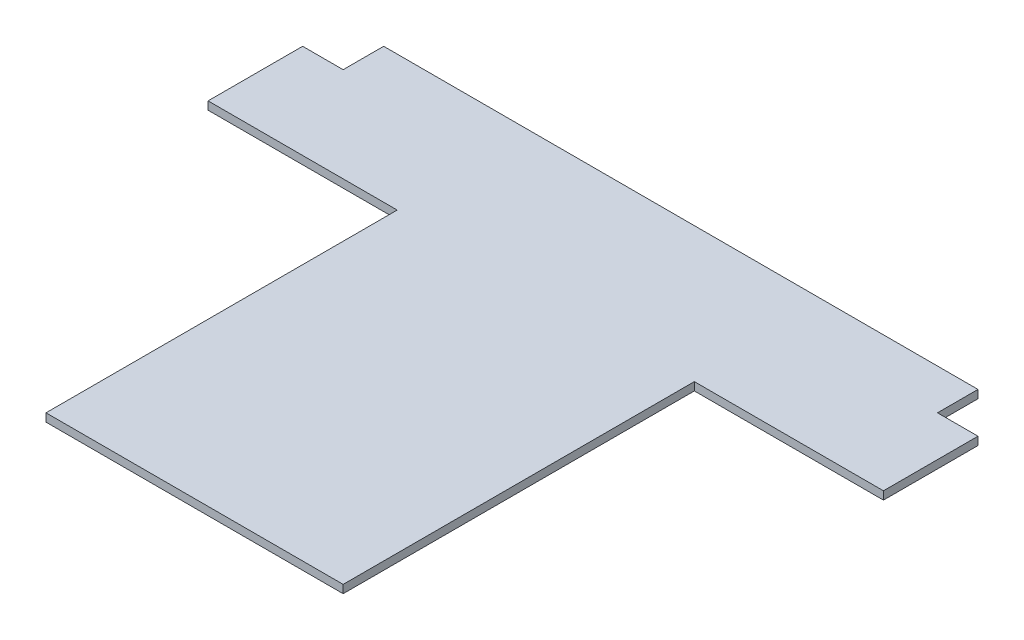
SolidWorks part; units mm, degrees
ref_plane "Plano frontal" through (0, 0, 0) normal (0, 0, 1) x (1, 0, 0)
ref_plane "Plano superior" through (0, 0, 0) normal (0, 1, 0) x (1, 0, 0)
ref_plane "Plano direito" through (0, 0, 0) normal (1, 0, 0) x (0, 0, -1)
sketch "Esboço1" plane through (0, 0, 0) normal (0, 1, 0) x (1, 0, 0)
  line L0 (-250, 80) -> (-250, 150)
  line L1 (-250, 150) -> (-220, 150)
  line L2 (-220, 150) -> (-220, 180)
  line L3 (-220, 180) -> (220, 180)
  line L4 (220, 180) -> (220, 150)
  line L5 (220, 150) -> (250, 150)
  line L6 (250, 150) -> (250, 80)
  line L7 (250, 80) -> (110, 80)
  line L8 (110, 80) -> (110, -180)
  line L9 (110, -180) -> (-110, -180)
  line L10 (-110, -180) -> (-110, 80)
  line L11 (-110, 80) -> (-250, 80)
  line L12 (0, 180) -> (0, -180) construction
  point P0 (0, -180)
  point P13 (0, 0)
  point P15 (0, 180)
  dimension "D1" = 30
  dimension "D2" = 440
  dimension "D3" = 220
  dimension "D4" = 360
  dimension "D5" = 100
extrude "Ressalto-extrusão1" add sketch "Esboço1" along normal blind 6
